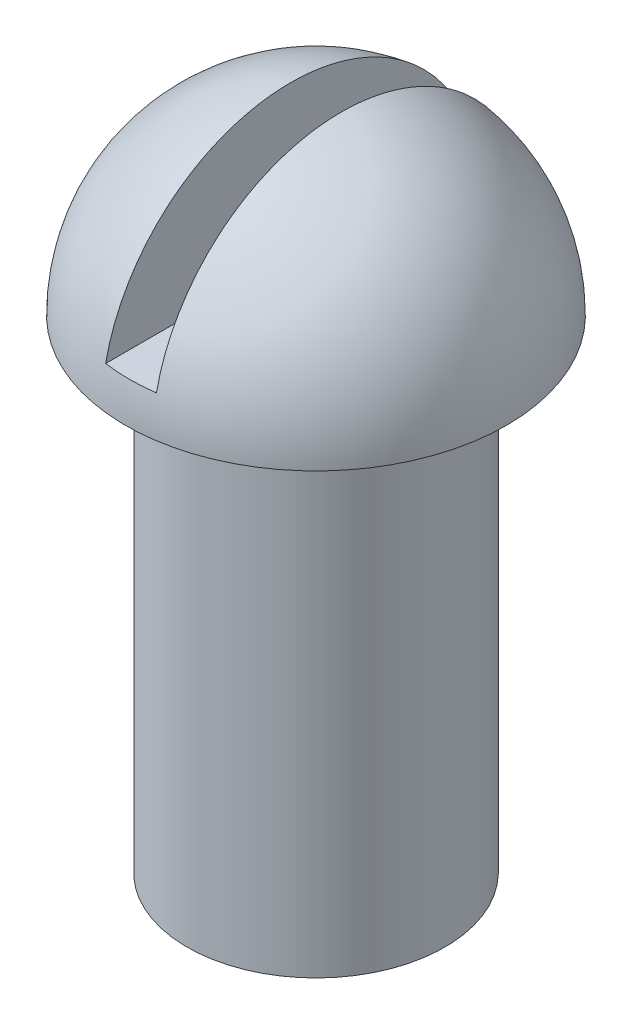
SolidWorks part; units mm, degrees
ref_plane "Front Plane" through (0, 0, 0) normal (0, 0, 1) x (1, 0, 0)
ref_plane "Top Plane" through (0, 0, 0) normal (0, 1, 0) x (1, 0, 0)
ref_plane "Right Plane" through (0, 0, 0) normal (1, 0, 0) x (0, 0, -1)
sketch "Sketch1" plane through (0, 0, 0) normal (0, 0, 1) x (1, 0, 0)
  line L0 (0, 53) -> (0, 0)
  line L1 (0, 0) -> (10.15, 0)
  line L2 (10.15, 0) -> (10.15, 38)
  line L3 (10.15, 38) -> (15, 38)
  arc A0 (15, 38) -> (0, 53) centre (0, 38) ccw
  dimension "D1" = 15
  dimension "D2" = 38
  dimension "D3" = 10.15
revolve "Revolve1" add sketch "Sketch1" angle 360 about L0
sketch "Sketch2" plane through (0, 0, 0) normal (0, 0, 1) x (1, 0, 0)
  line L0 (0, 0) -> (0, 41) construction
  line L1 (-2, 61.3252) -> (2, 61.3252)
  line L2 (-2, 61.3252) -> (-2, 41)
  line L3 (-2, 41) -> (2, 41)
  line L4 (2, 61.3252) -> (2, 41)
  line L5 (-10.15, 38) -> (10.15, 38) construction
  dimension "D1" = 4
  dimension "D2" = 3
extrude "Cut-Extrude1" cut sketch "Sketch2" against normal through all both and the other way through all
